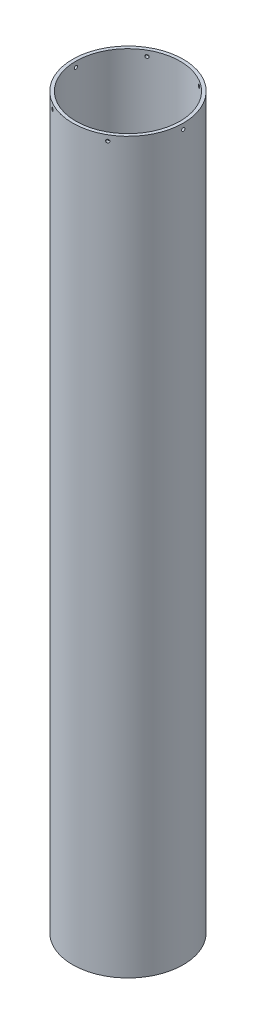
SolidWorks part; units mm, degrees
material "E-Glass Fiber"
ref_plane "Front Plane" through (0, 0, 0) normal (0, 0, 1) x (1, 0, 0)
ref_plane "Top Plane" through (0, 0, 0) normal (0, 1, 0) x (1, 0, 0)
ref_plane "Right Plane" through (0, 0, 0) normal (1, 0, 0) x (0, 0, -1)
sketch "Sketch1" plane through (0, 0, 0) normal (0, 1, 0) x (1, 0, 0)
  circle A4 centre (0, 0) radius 50.8
  circle A5 centre (0, 0) radius 53.975
  point P0 (0, 0)
  dimension "D1" = 101.6
  dimension "D2" = 3.175
extrude "Boss-Extrude1" add sketch "Sketch1" along normal blind 711.2
sketch "Sketch2" plane through (0, 0, 0) normal (1, 0, 0) x (0, 0, -1)
  line L0 (0, 711.2) -> (0, 705.8469) construction
  line L1 (50.8, 711.2) -> (-50.8, 711.2) construction
  circle A0 centre (0, 705.8469) radius 1.5875
  dimension "D2" = 3.175
  dimension "D1" = 5.353
extrude "Cut-Extrude1" cut sketch "Sketch2" against normal through all both and the other way through all
pattern_circular "CirPattern1" count 3 over 360 about axis through (0, 711.2, 0) along (0, 1, 0) of "Cut-Extrude1"
